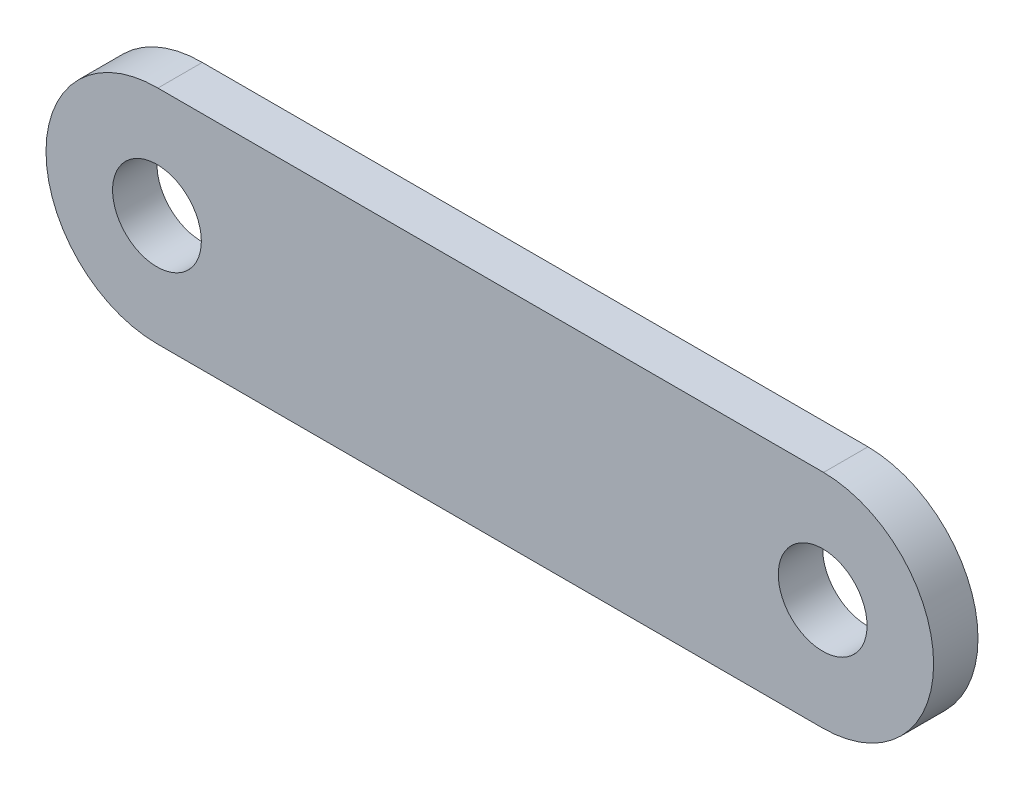
SolidWorks part; units mm, degrees
ref_plane "Front Plane" through (0, 0, 0) normal (0, 0, 1) x (1, 0, 0)
ref_plane "Top Plane" through (0, 0, 0) normal (0, 1, 0) x (1, 0, 0)
ref_plane "Right Plane" through (0, 0, 0) normal (1, 0, 0) x (0, 0, -1)
sketch "Sketch1" plane through (0, 0, 0) normal (0, 0, 1) x (1, 0, 0)
  line L0 (-14.9788, 2.4999) -> (0.0212, 2.4999)
  line L2 (-15, -2.5) -> (0, -2.5)
  circle A0 centre (0, 0) radius 1
  circle A1 centre (-15, 0) radius 1
  arc A2 (0, -2.5) -> (-0.0212, 2.4999) centre (0, 0) ccw
  arc A3 (-14.9788, 2.4999) -> (-15, -2.5) centre (-15, 0) ccw
  circle A4 centre (-15, 0) radius 2.5 construction
  circle A5 centre (0, 0) radius 2.5 construction
  point P12 (-20.9551, 0)
  point P14 (-16.4753, 0)
  point P15 (-14.4056, -2.5)
  dimension "D1" = 2
  dimension "D3" = 15
  dimension "D2" = 1.5
extrude "Boss-Extrude1" add sketch "Sketch1" along normal blind 1 contours L0 A3 L2 A2 A0 A1
